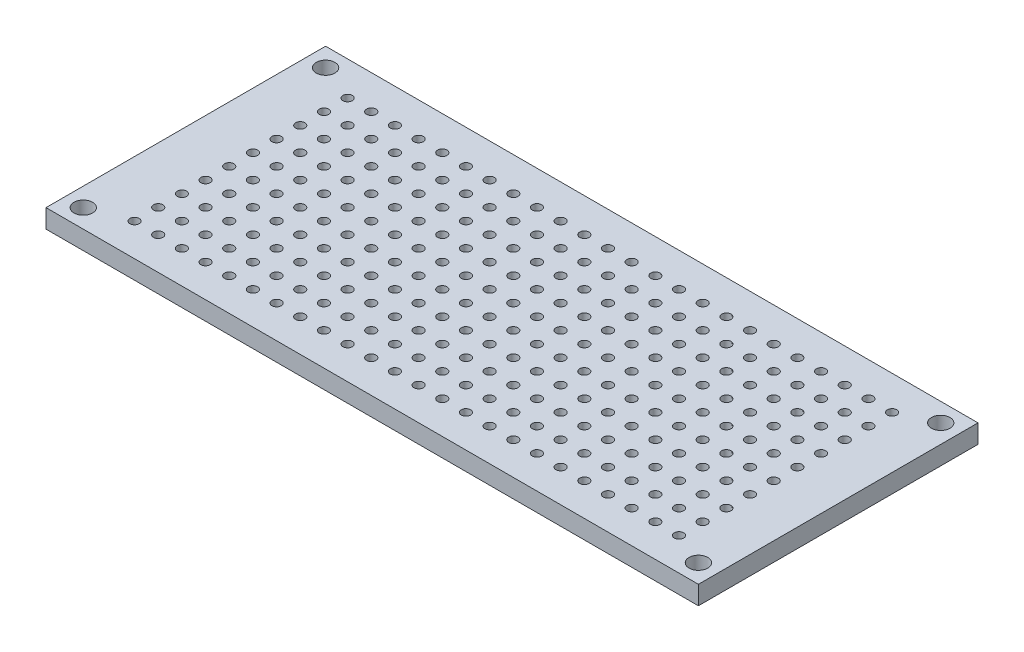
SolidWorks part; units mm, degrees
ref_plane "Спереди" through (0, 0, 0) normal (0, 0, 1) x (1, 0, 0)
ref_plane "Сверху" through (0, 0, 0) normal (0, 1, 0) x (1, 0, 0)
ref_plane "Справа" through (0, 0, 0) normal (1, 0, 0) x (0, 0, -1)
other "Configuration Table"
sketch "Эскиз1" plane through (0, 0, 0) normal (0, 1, 0) x (1, 0, 0)
  line L1 (35, -15) -> (-35, -15)
  line L2 (35, -15) -> (35, 15)
  line L3 (35, 15) -> (-35, 15)
  line L4 (-35, -15) -> (-35, 15)
  line L5 (35, -15) -> (-35, 15) construction
  line L6 (35, 15) -> (-35, -15) construction
  line L7 (33, -13) -> (-33, -13) construction
  line L8 (33, -13) -> (33, 13) construction
  line L9 (33, 13) -> (-33, 13) construction
  line L10 (-33, -13) -> (-33, 13) construction
  line L11 (33, -13) -> (-33, 13) construction
  line L12 (33, 13) -> (-33, -13) construction
  circle A0 centre (-33, 13) radius 1
  circle A1 centre (-33, -13) radius 1
  circle A2 centre (33, 13) radius 1
  circle A3 centre (33, -13) radius 1
  circle A4 centre (-29, -11.5) radius 0.5
  circle A5 centre (-26.46, -11.5) radius 0.5
  circle A6 centre (-23.92, -11.5) radius 0.5
  circle A7 centre (-21.38, -11.5) radius 0.5
  circle A8 centre (-18.84, -11.5) radius 0.5
  circle A9 centre (-16.3, -11.5) radius 0.5
  circle A10 centre (-13.76, -11.5) radius 0.5
  circle A11 centre (-11.22, -11.5) radius 0.5
  circle A12 centre (-8.68, -11.5) radius 0.5
  circle A13 centre (-6.14, -11.5) radius 0.5
  circle A14 centre (-3.6, -11.5) radius 0.5
  circle A15 centre (-1.06, -11.5) radius 0.5
  circle A16 centre (1.48, -11.5) radius 0.5
  circle A17 centre (4.02, -11.5) radius 0.5
  circle A18 centre (6.56, -11.5) radius 0.5
  circle A19 centre (9.1, -11.5) radius 0.5
  circle A20 centre (11.64, -11.5) radius 0.5
  circle A21 centre (14.18, -11.5) radius 0.5
  circle A22 centre (16.72, -11.5) radius 0.5
  circle A23 centre (19.26, -11.5) radius 0.5
  circle A24 centre (21.8, -11.5) radius 0.5
  circle A25 centre (24.34, -11.5) radius 0.5
  circle A26 centre (26.88, -11.5) radius 0.5
  circle A27 centre (29.42, -11.5) radius 0.5
  circle A28 centre (-26.46, -8.96) radius 0.5
  circle A29 centre (-23.92, -8.96) radius 0.5
  circle A30 centre (-21.38, -8.96) radius 0.5
  circle A31 centre (-18.84, -8.96) radius 0.5
  circle A32 centre (-16.3, -8.96) radius 0.5
  circle A33 centre (-13.76, -8.96) radius 0.5
  circle A34 centre (-11.22, -8.96) radius 0.5
  circle A35 centre (-8.68, -8.96) radius 0.5
  circle A36 centre (-6.14, -8.96) radius 0.5
  circle A37 centre (-3.6, -8.96) radius 0.5
  circle A38 centre (-1.06, -8.96) radius 0.5
  circle A39 centre (1.48, -8.96) radius 0.5
  circle A40 centre (4.02, -8.96) radius 0.5
  circle A41 centre (6.56, -8.96) radius 0.5
  circle A42 centre (9.1, -8.96) radius 0.5
  circle A43 centre (11.64, -8.96) radius 0.5
  circle A44 centre (14.18, -8.96) radius 0.5
  circle A45 centre (16.72, -8.96) radius 0.5
  circle A46 centre (19.26, -8.96) radius 0.5
  circle A47 centre (21.8, -8.96) radius 0.5
  circle A48 centre (24.34, -8.96) radius 0.5
  circle A49 centre (26.88, -8.96) radius 0.5
  circle A50 centre (29.42, -8.96) radius 0.5
  circle A51 centre (-26.46, -6.42) radius 0.5
  circle A52 centre (-23.92, -6.42) radius 0.5
  circle A53 centre (-21.38, -6.42) radius 0.5
  circle A54 centre (-18.84, -6.42) radius 0.5
  circle A55 centre (-16.3, -6.42) radius 0.5
  circle A56 centre (-13.76, -6.42) radius 0.5
  circle A57 centre (-11.22, -6.42) radius 0.5
  circle A58 centre (-8.68, -6.42) radius 0.5
  circle A59 centre (-6.14, -6.42) radius 0.5
  circle A60 centre (-3.6, -6.42) radius 0.5
  circle A61 centre (-1.06, -6.42) radius 0.5
  circle A62 centre (1.48, -6.42) radius 0.5
  circle A63 centre (4.02, -6.42) radius 0.5
  circle A64 centre (6.56, -6.42) radius 0.5
  circle A65 centre (9.1, -6.42) radius 0.5
  circle A66 centre (11.64, -6.42) radius 0.5
  circle A67 centre (14.18, -6.42) radius 0.5
  circle A68 centre (16.72, -6.42) radius 0.5
  circle A69 centre (19.26, -6.42) radius 0.5
  circle A70 centre (21.8, -6.42) radius 0.5
  circle A71 centre (24.34, -6.42) radius 0.5
  circle A72 centre (26.88, -6.42) radius 0.5
  circle A73 centre (29.42, -6.42) radius 0.5
  circle A74 centre (-26.46, -3.88) radius 0.5
  circle A75 centre (-23.92, -3.88) radius 0.5
  circle A76 centre (-21.38, -3.88) radius 0.5
  circle A77 centre (-18.84, -3.88) radius 0.5
  circle A78 centre (-16.3, -3.88) radius 0.5
  circle A79 centre (-13.76, -3.88) radius 0.5
  circle A80 centre (-11.22, -3.88) radius 0.5
  circle A81 centre (-8.68, -3.88) radius 0.5
  circle A82 centre (-6.14, -3.88) radius 0.5
  circle A83 centre (-3.6, -3.88) radius 0.5
  circle A84 centre (-1.06, -3.88) radius 0.5
  circle A85 centre (1.48, -3.88) radius 0.5
  circle A86 centre (4.02, -3.88) radius 0.5
  circle A87 centre (6.56, -3.88) radius 0.5
  circle A88 centre (9.1, -3.88) radius 0.5
  circle A89 centre (11.64, -3.88) radius 0.5
  circle A90 centre (14.18, -3.88) radius 0.5
  circle A91 centre (16.72, -3.88) radius 0.5
  circle A92 centre (19.26, -3.88) radius 0.5
  circle A93 centre (21.8, -3.88) radius 0.5
  circle A94 centre (24.34, -3.88) radius 0.5
  circle A95 centre (26.88, -3.88) radius 0.5
  circle A96 centre (29.42, -3.88) radius 0.5
  circle A97 centre (-26.46, -1.34) radius 0.5
  circle A98 centre (-23.92, -1.34) radius 0.5
  circle A99 centre (-21.38, -1.34) radius 0.5
  circle A100 centre (-18.84, -1.34) radius 0.5
  circle A101 centre (-16.3, -1.34) radius 0.5
  circle A102 centre (-13.76, -1.34) radius 0.5
  circle A103 centre (-11.22, -1.34) radius 0.5
  circle A104 centre (-8.68, -1.34) radius 0.5
  circle A105 centre (-6.14, -1.34) radius 0.5
  circle A106 centre (-3.6, -1.34) radius 0.5
  circle A107 centre (-1.06, -1.34) radius 0.5
  circle A108 centre (1.48, -1.34) radius 0.5
  circle A109 centre (4.02, -1.34) radius 0.5
  circle A110 centre (6.56, -1.34) radius 0.5
  circle A111 centre (9.1, -1.34) radius 0.5
  circle A112 centre (11.64, -1.34) radius 0.5
  circle A113 centre (14.18, -1.34) radius 0.5
  circle A114 centre (16.72, -1.34) radius 0.5
  circle A115 centre (19.26, -1.34) radius 0.5
  circle A116 centre (21.8, -1.34) radius 0.5
  circle A117 centre (24.34, -1.34) radius 0.5
  circle A118 centre (26.88, -1.34) radius 0.5
  circle A119 centre (29.42, -1.34) radius 0.5
  circle A120 centre (-26.46, 1.2) radius 0.5
  circle A121 centre (-23.92, 1.2) radius 0.5
  circle A122 centre (-21.38, 1.2) radius 0.5
  circle A123 centre (-18.84, 1.2) radius 0.5
  circle A124 centre (-16.3, 1.2) radius 0.5
  circle A125 centre (-13.76, 1.2) radius 0.5
  circle A126 centre (-11.22, 1.2) radius 0.5
  circle A127 centre (-8.68, 1.2) radius 0.5
  circle A128 centre (-6.14, 1.2) radius 0.5
  circle A129 centre (-3.6, 1.2) radius 0.5
  circle A130 centre (-1.06, 1.2) radius 0.5
  circle A131 centre (1.48, 1.2) radius 0.5
  circle A132 centre (4.02, 1.2) radius 0.5
  circle A133 centre (6.56, 1.2) radius 0.5
  circle A134 centre (9.1, 1.2) radius 0.5
  circle A135 centre (11.64, 1.2) radius 0.5
  circle A136 centre (14.18, 1.2) radius 0.5
  circle A137 centre (16.72, 1.2) radius 0.5
  circle A138 centre (19.26, 1.2) radius 0.5
  circle A139 centre (21.8, 1.2) radius 0.5
  circle A140 centre (24.34, 1.2) radius 0.5
  circle A141 centre (26.88, 1.2) radius 0.5
  circle A142 centre (29.42, 1.2) radius 0.5
  circle A143 centre (-26.46, 3.74) radius 0.5
  circle A144 centre (-23.92, 3.74) radius 0.5
  circle A145 centre (-21.38, 3.74) radius 0.5
  circle A146 centre (-18.84, 3.74) radius 0.5
  circle A147 centre (-16.3, 3.74) radius 0.5
  circle A148 centre (-13.76, 3.74) radius 0.5
  circle A149 centre (-11.22, 3.74) radius 0.5
  circle A150 centre (-8.68, 3.74) radius 0.5
  circle A151 centre (-6.14, 3.74) radius 0.5
  circle A152 centre (-3.6, 3.74) radius 0.5
  circle A153 centre (-1.06, 3.74) radius 0.5
  circle A154 centre (1.48, 3.74) radius 0.5
  circle A155 centre (4.02, 3.74) radius 0.5
  circle A156 centre (6.56, 3.74) radius 0.5
  circle A157 centre (9.1, 3.74) radius 0.5
  circle A158 centre (11.64, 3.74) radius 0.5
  circle A159 centre (14.18, 3.74) radius 0.5
  circle A160 centre (16.72, 3.74) radius 0.5
  circle A161 centre (19.26, 3.74) radius 0.5
  circle A162 centre (21.8, 3.74) radius 0.5
  circle A163 centre (24.34, 3.74) radius 0.5
  circle A164 centre (26.88, 3.74) radius 0.5
  circle A165 centre (29.42, 3.74) radius 0.5
  circle A166 centre (-26.46, 6.28) radius 0.5
  circle A167 centre (-23.92, 6.28) radius 0.5
  circle A168 centre (-21.38, 6.28) radius 0.5
  circle A169 centre (-18.84, 6.28) radius 0.5
  circle A170 centre (-16.3, 6.28) radius 0.5
  circle A171 centre (-13.76, 6.28) radius 0.5
  circle A172 centre (-11.22, 6.28) radius 0.5
  circle A173 centre (-8.68, 6.28) radius 0.5
  circle A174 centre (-6.14, 6.28) radius 0.5
  circle A175 centre (-3.6, 6.28) radius 0.5
  circle A176 centre (-1.06, 6.28) radius 0.5
  circle A177 centre (1.48, 6.28) radius 0.5
  circle A178 centre (4.02, 6.28) radius 0.5
  circle A179 centre (6.56, 6.28) radius 0.5
  circle A180 centre (9.1, 6.28) radius 0.5
  circle A181 centre (11.64, 6.28) radius 0.5
  circle A182 centre (14.18, 6.28) radius 0.5
  circle A183 centre (16.72, 6.28) radius 0.5
  circle A184 centre (19.26, 6.28) radius 0.5
  circle A185 centre (21.8, 6.28) radius 0.5
  circle A186 centre (24.34, 6.28) radius 0.5
  circle A187 centre (26.88, 6.28) radius 0.5
  circle A188 centre (29.42, 6.28) radius 0.5
  circle A189 centre (-26.46, 8.82) radius 0.5
  circle A190 centre (-23.92, 8.82) radius 0.5
  circle A191 centre (-21.38, 8.82) radius 0.5
  circle A192 centre (-18.84, 8.82) radius 0.5
  circle A193 centre (-16.3, 8.82) radius 0.5
  circle A194 centre (-13.76, 8.82) radius 0.5
  circle A195 centre (-11.22, 8.82) radius 0.5
  circle A196 centre (-8.68, 8.82) radius 0.5
  circle A197 centre (-6.14, 8.82) radius 0.5
  circle A198 centre (-3.6, 8.82) radius 0.5
  circle A199 centre (-1.06, 8.82) radius 0.5
  circle A200 centre (1.48, 8.82) radius 0.5
  circle A201 centre (4.02, 8.82) radius 0.5
  circle A202 centre (6.56, 8.82) radius 0.5
  circle A203 centre (9.1, 8.82) radius 0.5
  circle A204 centre (11.64, 8.82) radius 0.5
  circle A205 centre (14.18, 8.82) radius 0.5
  circle A206 centre (16.72, 8.82) radius 0.5
  circle A207 centre (19.26, 8.82) radius 0.5
  circle A208 centre (21.8, 8.82) radius 0.5
  circle A209 centre (24.34, 8.82) radius 0.5
  circle A210 centre (26.88, 8.82) radius 0.5
  circle A211 centre (29.42, 8.82) radius 0.5
  circle A212 centre (-26.46, 11.36) radius 0.5
  circle A213 centre (-23.92, 11.36) radius 0.5
  circle A214 centre (-21.38, 11.36) radius 0.5
  circle A215 centre (-18.84, 11.36) radius 0.5
  circle A216 centre (-16.3, 11.36) radius 0.5
  circle A217 centre (-13.76, 11.36) radius 0.5
  circle A218 centre (-11.22, 11.36) radius 0.5
  circle A219 centre (-8.68, 11.36) radius 0.5
  circle A220 centre (-6.14, 11.36) radius 0.5
  circle A221 centre (-3.6, 11.36) radius 0.5
  circle A222 centre (-1.06, 11.36) radius 0.5
  circle A223 centre (1.48, 11.36) radius 0.5
  circle A224 centre (4.02, 11.36) radius 0.5
  circle A225 centre (6.56, 11.36) radius 0.5
  circle A226 centre (9.1, 11.36) radius 0.5
  circle A227 centre (11.64, 11.36) radius 0.5
  circle A228 centre (14.18, 11.36) radius 0.5
  circle A229 centre (16.72, 11.36) radius 0.5
  circle A230 centre (19.26, 11.36) radius 0.5
  circle A231 centre (21.8, 11.36) radius 0.5
  circle A232 centre (24.34, 11.36) radius 0.5
  circle A233 centre (26.88, 11.36) radius 0.5
  circle A234 centre (29.42, 11.36) radius 0.5
  circle A235 centre (-29, -8.96) radius 0.5
  circle A236 centre (-29, -6.42) radius 0.5
  circle A237 centre (-29, -3.88) radius 0.5
  circle A238 centre (-29, -1.34) radius 0.5
  circle A239 centre (-29, 1.2) radius 0.5
  circle A240 centre (-29, 3.74) radius 0.5
  circle A241 centre (-29, 6.28) radius 0.5
  circle A242 centre (-29, 8.82) radius 0.5
  circle A243 centre (-29, 11.36) radius 0.5
  point P0 (0, 0)
  point P6 (0, 0)
  dimension "D5" = 2
  dimension "D8" = 1
  dimension "D1" = 70
  dimension "D2" = 30
  dimension "D3" = 66
  dimension "D4" = 26
  dimension "D6" = 6
  dimension "D7" = 3.5
  dimension "D9" = 24
  dimension "D10" = 10
extrude "Бобышка-Вытянуть1" add sketch "Эскиз1" along normal blind 2
